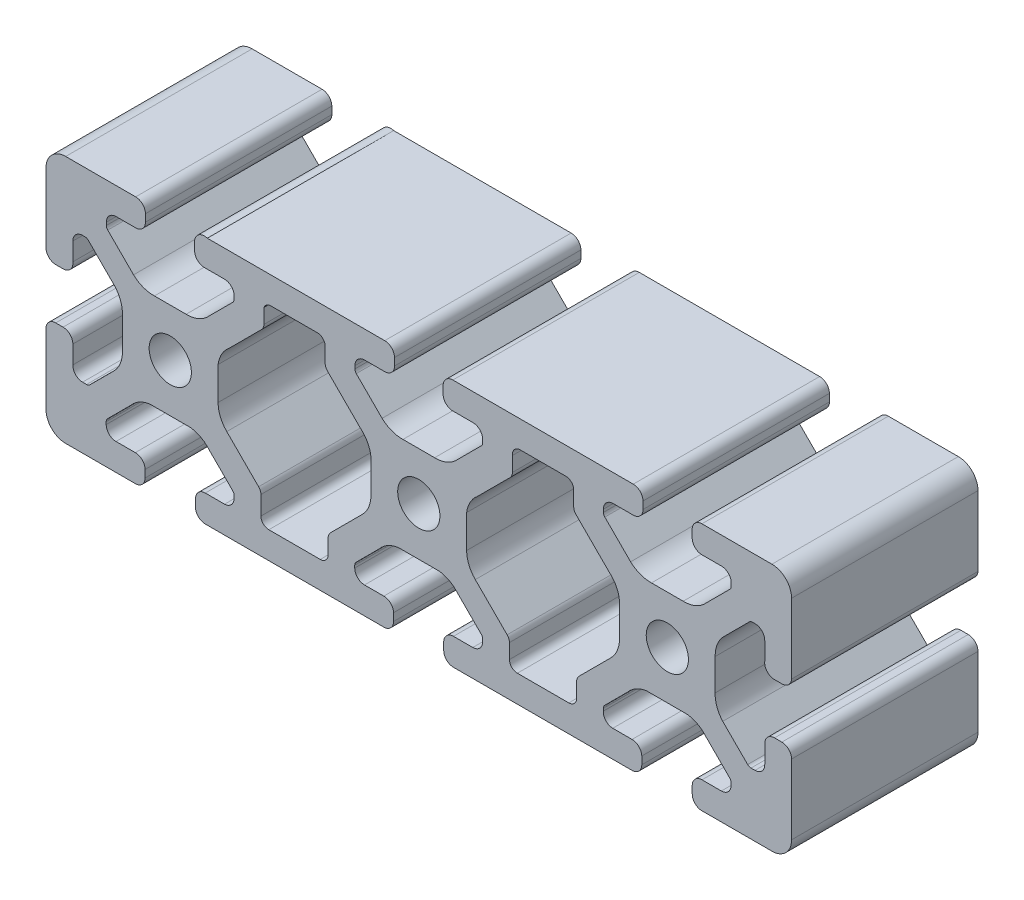
SolidWorks part; units mm, degrees
material "6061 Alloy"
ref_plane "Front Plane" through (0, 0, 0) normal (0, 0, 1) x (1, 0, 0)
ref_plane "Top Plane" through (0, 0, 0) normal (0, 1, 0) x (1, 0, 0)
ref_plane "Right Plane" through (0, 0, 0) normal (1, 0, 0) x (0, 0, -1)
sketch "Sketch1" plane through (0, 0, 0) normal (0, 0, 1) x (1, 0, 0)
  line L0 (-66.9907, 0) -> (65.4005, 0) construction
  line L128 (-34.0397, 20) -> (-5.4835, 20)
  line L129 (-36.0865, 17.2476) -> (-36.0865, 18.4276)
  line L130 (-31.285, 15.68) -> (-34.5165, 15.68)
  line L131 (-29.715, 13.6545) -> (-29.715, 14.11)
  line L132 (-16.3366, 15.68) -> (-23.6634, 15.68)
  line L133 (-24.9334, 14.9061) -> (-24.9334, 12.538)
  line L134 (-25.3054, 11.6399) -> (-30.5988, 6.3465)
  line L135 (-32.3, 3.2591) -> (-32.3, -2.0252)
  line L136 (-14.009, -20) -> (-21.7801, -20)
  line L137 (-19.7616, 20) -> (-19.7616, -25.1394) construction
  line L138 (-24.1394, -15.68) -> (-15.8606, -15.68)
  line L139 (-25.4094, -11.4093) -> (-25.4094, -14.41)
  line L140 (-30.9088, -5.384) -> (-25.7814, -10.5113)
  line L142 (-29.9376, 13.1171) -> (-34.0919, 8.9628)
  line L143 (-37.4506, 7.7) -> (-42.5494, 7.7)
  line L144 (-45.9081, 8.9628) -> (-50.0624, 13.1171)
  line L145 (-50.285, 13.6545) -> (-50.285, 14.11)
  line L146 (-48.715, 15.68) -> (-45.5696, 15.68)
  line L147 (-43.9996, 17.25) -> (-43.9996, 18.43)
  line L148 (-45.5696, 20) -> (-53, 20)
  line L149 (-53, 20) -> (-56.83, 20)
  line L150 (-60, 16.8406) -> (-60, 13.0106)
  line L151 (-60, 13.0106) -> (-60, 5.5825)
  line L152 (-58.3243, 4.1259) -> (-57.1443, 4.1259)
  line L153 (-55.68, 5.8839) -> (-55.68, 8.7865)
  line L154 (-54.11, 10.3565) -> (-53.726, 10.3565)
  line L155 (-53.1886, 10.1339) -> (-49.0111, 5.9564)
  line L156 (-47.7, 2.571) -> (-47.7, -2.502)
  line L157 (-48.9155, -5.8608) -> (-52.9291, -9.8744)
  line L158 (-53.4665, -10.097) -> (-54.111, -10.097)
  line L159 (-55.68, -8.4722) -> (-55.68, -5.5696)
  line L160 (-57.25, -3.9996) -> (-58.43, -3.9996)
  line L161 (-60, -5.5696) -> (-60, -13)
  line L162 (-60, -13) -> (-60, -16.83)
  line L163 (-57.0574, -20) -> (-53.2274, -20)
  line L164 (-53.2274, -20) -> (-45.797, -20)
  line L165 (-44.06, -18.4389) -> (-44.06, -17.25)
  line L166 (-45.63, -15.68) -> (-48.7404, -15.68)
  line L167 (-50.3104, -14.11) -> (-50.3104, -13.7197)
  line L168 (-50.0878, -13.1823) -> (-46.3105, -9.405)
  line L169 (-43.3425, -7.7407) -> (-36.6594, -7.7407)
  line L170 (-33.6914, -9.405) -> (-29.9611, -13.1353)
  line L171 (-29.7385, -13.6727) -> (-29.7385, -14.1108)
  line L172 (-31.2596, -15.68) -> (-34.37, -15.68)
  line L173 (-35.94, -17.25) -> (-35.94, -18.43)
  line L174 (-34.37, -20) -> (-25.991, -20)
  line L175 (-25.991, -20) -> (-21.7801, -20)
  line L176 (-5.63, -20) -> (-14.009, -20)
  line L177 (-4.06, -17.2093) -> (-4.06, -18.43)
  line L178 (-8.7404, -15.68) -> (-5.63, -15.68)
  line L179 (-10.3104, -13.7197) -> (-10.3104, -14.11)
  line L180 (-6.3105, -9.405) -> (-10.0878, -13.1823)
  line L181 (3.3406, -7.7407) -> (-3.3425, -7.7407)
  line L182 (29.9376, 13.1171) -> (34.0919, 8.9628)
  line L183 (3.9116, 17.25) -> (3.9116, 18.43)
  line L184 (8.715, 15.68) -> (5.4816, 15.68)
  line L185 (10.285, 13.6545) -> (10.285, 14.11)
  line L186 (15.0666, 14.2735) -> (15.0666, 11.9054)
  line L187 (14.6946, 11.0074) -> (9.4012, 5.7139)
  line L188 (7.7, 2.6265) -> (7.7, -2.6578)
  line L189 (14.5906, -12.0419) -> (14.5906, -14.41)
  line L190 (9.0912, -6.0165) -> (14.2186, -11.1439)
  line L191 (10.0624, 13.1171) -> (5.9081, 8.9628)
  line L192 (6.3086, -9.405) -> (10.037, -13.1334)
  line L193 (10.2596, -13.6708) -> (10.2596, -14.11)
  line L194 (8.6896, -15.68) -> (5.5792, -15.68)
  line L195 (4.0092, -17.2093) -> (4.0092, -18.43)
  line L196 (5.5792, -20) -> (13.9582, -20)
  line L197 (25.9402, -20) -> (21.7292, -20)
  line L198 (34.3192, -20) -> (25.9402, -20)
  line L199 (35.8892, -17.2093) -> (35.8892, -18.43)
  line L200 (31.2088, -15.68) -> (34.3192, -15.68)
  line L201 (29.6886, -13.6708) -> (29.6886, -14.0552)
  line L202 (33.6397, -9.405) -> (29.9112, -13.1334)
  line L203 (43.2907, -7.7407) -> (36.6076, -7.7407)
  line L204 (50.036, -13.1823) -> (46.2587, -9.405)
  line L205 (50.2586, -14.0552) -> (50.2586, -13.7197)
  line L206 (45.5792, -15.68) -> (48.6896, -15.68)
  line L207 (-2.5494, 7.7) -> (2.5494, 7.7)
  line L208 (-10.0624, 13.1171) -> (-5.9081, 8.9628)
  line L209 (-9.0912, -6.0165) -> (-14.2186, -11.1439)
  line L210 (-14.5906, -12.0419) -> (-14.5906, -14.41)
  line L211 (-7.7, 2.6265) -> (-7.7, -2.6578)
  line L212 (-14.6946, 11.1439) -> (-9.4012, 5.8505)
  line L213 (-15.0666, 14.41) -> (-15.0666, 12.0419)
  line L214 (-10.285, 13.6545) -> (-10.285, 14.11)
  line L215 (-8.715, 15.68) -> (-5.4835, 15.68)
  line L216 (-3.9135, 17.25) -> (-3.9135, 18.43)
  line L217 (-40, 24.8708) -> (-40, -18.43) construction
  line L218 (0, 29.4355) -> (0, -23.1087) construction
  line L219 (-23.0962, 16.9038) -> (-63.6857, -23.6857) construction
  line L220 (-56.2671, 16.2671) -> (-22.7875, -17.2125) construction
  line L221 (44.0092, -18.4389) -> (44.0092, -17.2093)
  line L222 (53.1766, -20) -> (45.7462, -20)
  line L223 (57.0066, -20) -> (53.1766, -20)
  line L224 (60, -13) -> (60, -16.83)
  line L225 (60, -5.5696) -> (60, -13)
  line L226 (57.25, -3.9996) -> (58.43, -3.9996)
  line L227 (55.68, -8.4722) -> (55.68, -5.5696)
  line L228 (53.4665, -10.097) -> (54.111, -10.097)
  line L229 (48.9155, -5.8608) -> (52.9291, -9.8744)
  line L230 (47.7, 2.571) -> (47.7, -2.502)
  line L231 (53.1886, 10.1339) -> (49.0111, 5.9564)
  line L232 (54.11, 10.3565) -> (53.726, 10.3565)
  line L233 (55.68, 5.8839) -> (55.68, 8.7865)
  line L234 (58.3243, 4.1259) -> (57.1443, 4.1259)
  line L235 (60, 13.0106) -> (60, 5.5825)
  line L236 (60, 16.8406) -> (60, 13.0106)
  line L237 (53, 20) -> (56.83, 20)
  line L238 (45.5696, 20) -> (53, 20)
  line L239 (43.9996, 17.25) -> (43.9996, 18.43)
  line L240 (48.715, 15.68) -> (45.5696, 15.68)
  line L241 (50.285, 13.6545) -> (50.285, 14.11)
  line L242 (45.9081, 8.9628) -> (50.0624, 13.1171)
  line L243 (37.4506, 7.7) -> (42.5494, 7.7)
  line L244 (30.9088, -6.0165) -> (25.7814, -11.1439)
  line L245 (25.4094, -12.0419) -> (25.4094, -14.41)
  line L246 (24.1394, -15.68) -> (15.8606, -15.68)
  line L247 (13.9582, -20) -> (21.7292, -20)
  line L248 (32.3, 2.6265) -> (32.3, -2.6578)
  line L249 (25.3054, 11.1439) -> (30.5988, 5.8505)
  line L250 (24.9334, 14.41) -> (24.9334, 12.0419)
  line L251 (16.3366, 15.68) -> (23.6634, 15.68)
  line L252 (29.715, 13.6545) -> (29.715, 14.11)
  line L253 (31.285, 15.68) -> (34.5165, 15.68)
  line L254 (36.0865, 17.25) -> (36.0865, 18.43)
  line L255 (34.5165, 20) -> (5.4816, 20)
  arc A111 (-36.0865, 18.4276) -> (-34.0397, 20) centre (-34.5184, 18.5048) cw
  circle A112 centre (-40, 0) radius 3.4
  arc A113 (-34.5165, 15.68) -> (-36.0865, 17.2476) centre (-34.5165, 17.25) cw
  arc A114 (-31.285, 15.68) -> (-29.715, 14.11) centre (-31.285, 14.11) cw
  arc A115 (-29.715, 13.6545) -> (-29.9376, 13.1171) centre (-30.475, 13.6545) cw
  arc A116 (-32.3, -2.0252) -> (-30.9088, -5.384) centre (-27.55, -2.0252) ccw
  arc A117 (-23.6634, 15.68) -> (-24.9334, 14.9061) centre (-23.7626, 14.4139) ccw
  arc A118 (-25.3054, 11.6399) -> (-24.9334, 12.538) centre (-26.2034, 12.538) ccw
  arc A119 (-30.5988, 6.3465) -> (-32.3, 3.2591) centre (-27.5862, 2.6741) ccw
  arc A120 (-25.4094, -14.41) -> (-24.1394, -15.68) centre (-24.1394, -14.41) ccw
  arc A121 (-25.4094, -11.4093) -> (-25.7814, -10.5113) centre (-26.6794, -11.4093) ccw
  arc A122 (-37.4506, 7.7) -> (-34.0919, 8.9628) centre (-37.3191, 12.4482) ccw
  arc A123 (-45.9081, 8.9628) -> (-42.5494, 7.7) centre (-42.6809, 12.4482) ccw
  arc A124 (-50.285, 13.6545) -> (-50.0624, 13.1171) centre (-49.525, 13.6545) ccw
  arc A125 (-48.715, 15.68) -> (-50.285, 14.11) centre (-48.715, 14.11) ccw
  arc A126 (-45.5696, 15.68) -> (-43.9996, 17.25) centre (-45.5696, 17.25) ccw
  arc A127 (-43.9996, 18.43) -> (-45.5696, 20) centre (-45.5696, 18.43) ccw
  arc A128 (-56.83, 20) -> (-60, 16.8406) centre (-56.83, 16.83) ccw
  arc A129 (-60, 5.5825) -> (-58.3243, 4.1259) centre (-58.4338, 5.692) ccw
  arc A130 (-57.1443, 4.1259) -> (-55.68, 5.8839) centre (-57.2384, 5.693) ccw
  arc A131 (-54.11, 10.3565) -> (-55.68, 8.7865) centre (-54.11, 8.7865) ccw
  arc A132 (-53.1886, 10.1339) -> (-53.726, 10.3565) centre (-53.726, 9.5965) ccw
  arc A133 (-47.7, 2.571) -> (-49.0111, 5.9564) centre (-52.4488, 2.6785) ccw
  arc A134 (-48.9155, -5.8608) -> (-47.7, -2.502) centre (-52.4465, -2.6836) ccw
  arc A135 (-53.4665, -10.097) -> (-52.9291, -9.8744) centre (-53.4665, -9.337) ccw
  arc A136 (-55.68, -8.4722) -> (-54.111, -10.097) centre (-54.111, -8.527) ccw
  arc A137 (-55.68, -5.5696) -> (-57.25, -3.9996) centre (-57.25, -5.5696) ccw
  arc A138 (-58.43, -3.9996) -> (-60, -5.5696) centre (-58.43, -5.5696) ccw
  arc A139 (-60, -16.83) -> (-57.0574, -20) centre (-56.83, -16.8382) ccw
  arc A140 (-45.797, -20) -> (-44.06, -18.4389) centre (-45.63, -18.4389) ccw
  arc A141 (-44.06, -17.25) -> (-45.63, -15.68) centre (-45.63, -17.25) ccw
  arc A142 (-50.3104, -14.11) -> (-48.7404, -15.68) centre (-48.7404, -14.11) ccw
  arc A143 (-50.0878, -13.1823) -> (-50.3104, -13.7197) centre (-49.5504, -13.7197) ccw
  arc A144 (-43.3425, -7.7407) -> (-46.3105, -9.405) centre (-42.6575, -12.4411) ccw
  arc A145 (-33.6914, -9.405) -> (-36.6594, -7.7407) centre (-37.3444, -12.4411) ccw
  arc A146 (-29.7385, -13.6727) -> (-29.9611, -13.1353) centre (-30.4985, -13.6727) ccw
  arc A147 (-31.2596, -15.68) -> (-29.7385, -14.1108) centre (-31.3085, -14.1108) ccw
  arc A148 (-34.37, -15.68) -> (-35.94, -17.25) centre (-34.37, -17.25) ccw
  arc A149 (-35.94, -18.43) -> (-34.37, -20) centre (-34.37, -18.43) ccw
  arc A150 (-4.06, -18.43) -> (-5.63, -20) centre (-5.63, -18.43) cw
  arc A151 (-5.63, -15.68) -> (-4.06, -17.2093) centre (-5.6295, -17.25) cw
  arc A152 (-8.7404, -15.68) -> (-10.3104, -14.11) centre (-8.7404, -14.11) cw
  arc A153 (-10.3104, -13.7197) -> (-10.0878, -13.1823) centre (-9.5504, -13.7197) cw
  arc A154 (-6.3105, -9.405) -> (-3.3425, -7.7407) centre (-2.6575, -12.4411) cw
  arc A155 (3.9116, 18.43) -> (5.4816, 20) centre (5.4816, 18.43) cw
  arc A156 (5.4816, 15.68) -> (3.9116, 17.25) centre (5.4816, 17.25) cw
  arc A157 (8.715, 15.68) -> (10.285, 14.11) centre (8.715, 14.11) cw
  arc A158 (10.285, 13.6545) -> (10.0624, 13.1171) centre (9.525, 13.6545) cw
  arc A159 (7.7, -2.6578) -> (9.0912, -6.0165) centre (12.45, -2.6578) ccw
  arc A160 (16.3366, 15.68) -> (15.0666, 14.2735) centre (16.3292, 14.41) ccw
  arc A161 (14.6946, 11.0074) -> (15.0666, 11.9054) centre (13.7966, 11.9054) ccw
  arc A162 (9.4012, 5.7139) -> (7.7, 2.6265) centre (12.4138, 2.0415) ccw
  arc A163 (14.5906, -14.41) -> (15.8606, -15.68) centre (15.8606, -14.41) ccw
  arc A164 (14.5906, -12.0419) -> (14.2186, -11.1439) centre (13.3206, -12.0419) ccw
  arc A165 (2.5494, 7.7) -> (5.9081, 8.9628) centre (2.6809, 12.4482) ccw
  arc A166 (6.3086, -9.405) -> (3.3406, -7.7407) centre (2.6556, -12.4411) ccw
  arc A167 (10.2596, -13.6708) -> (10.037, -13.1334) centre (9.4996, -13.6708) ccw
  arc A168 (8.6896, -15.68) -> (10.2596, -14.11) centre (8.6896, -14.11) ccw
  arc A169 (5.5792, -15.68) -> (4.0092, -17.2093) centre (5.5787, -17.25) ccw
  arc A170 (4.0092, -18.43) -> (5.5792, -20) centre (5.5792, -18.43) ccw
  arc A171 (35.8892, -18.43) -> (34.3192, -20) centre (34.3192, -18.43) cw
  arc A172 (34.3192, -15.68) -> (35.8892, -17.2093) centre (34.3197, -17.25) cw
  arc A173 (31.2088, -15.68) -> (29.6886, -14.0552) centre (31.2577, -14.1108) cw
  arc A174 (29.6886, -13.6708) -> (29.9112, -13.1334) centre (30.4486, -13.6708) cw
  arc A175 (33.6397, -9.405) -> (36.6076, -7.7407) centre (37.2927, -12.4411) cw
  arc A176 (43.2907, -7.7407) -> (46.2587, -9.405) centre (42.6057, -12.4411) cw
  arc A177 (-2.5494, 7.7) -> (-5.9081, 8.9628) centre (-2.6809, 12.4482) cw
  arc A178 (-14.5906, -12.0419) -> (-14.2186, -11.1439) centre (-13.3206, -12.0419) cw
  arc A179 (-14.5906, -14.41) -> (-15.8606, -15.68) centre (-15.8606, -14.41) cw
  arc A180 (-9.4012, 5.8505) -> (-7.7, 2.6265) centre (-12.43, 2.1914) cw
  arc A181 (-14.6946, 11.1439) -> (-15.0666, 12.0419) centre (-13.7966, 12.0419) cw
  arc A182 (-16.3366, 15.68) -> (-15.0666, 14.41) centre (-16.3366, 14.41) cw
  arc A183 (-7.7, -2.6578) -> (-9.0912, -6.0165) centre (-12.45, -2.6578) cw
  arc A184 (-10.285, 13.6545) -> (-10.0624, 13.1171) centre (-9.525, 13.6545) ccw
  arc A185 (-8.715, 15.68) -> (-10.285, 14.11) centre (-8.715, 14.11) ccw
  arc A186 (-5.4835, 15.68) -> (-3.9135, 17.25) centre (-5.4835, 17.25) ccw
  circle A187 centre (0, 0) radius 3.4
  arc A188 (-3.9135, 18.43) -> (-5.4835, 20) centre (-5.4835, 18.43) ccw
  arc A189 (50.036, -13.1823) -> (50.2586, -13.7197) centre (49.4986, -13.7197) cw
  arc A190 (50.2586, -14.0552) -> (48.6896, -15.68) centre (48.6896, -14.11) cw
  arc A191 (44.0092, -17.2093) -> (45.5792, -15.68) centre (45.5787, -17.25) cw
  arc A192 (45.7462, -20) -> (44.0092, -18.4389) centre (45.5792, -18.4389) cw
  arc A193 (60, -16.83) -> (57.0066, -20) centre (56.83, -16.8349) cw
  arc A194 (58.43, -3.9996) -> (60, -5.5696) centre (58.43, -5.5696) cw
  arc A195 (55.68, -5.5696) -> (57.25, -3.9996) centre (57.25, -5.5696) cw
  arc A196 (55.68, -8.4722) -> (54.111, -10.097) centre (54.111, -8.527) cw
  arc A197 (53.4665, -10.097) -> (52.9291, -9.8744) centre (53.4665, -9.337) cw
  arc A198 (48.9155, -5.8608) -> (47.7, -2.502) centre (52.4465, -2.6836) cw
  arc A199 (47.7, 2.571) -> (49.0111, 5.9564) centre (52.4488, 2.6785) cw
  arc A200 (53.1886, 10.1339) -> (53.726, 10.3565) centre (53.726, 9.5965) cw
  arc A201 (54.11, 10.3565) -> (55.68, 8.7865) centre (54.11, 8.7865) cw
  arc A202 (57.1443, 4.1259) -> (55.68, 5.8839) centre (57.2384, 5.693) cw
  arc A203 (60, 5.5825) -> (58.3243, 4.1259) centre (58.4338, 5.692) cw
  arc A204 (56.83, 20) -> (60, 16.8406) centre (56.83, 16.83) cw
  arc A205 (43.9996, 18.43) -> (45.5696, 20) centre (45.5696, 18.43) cw
  arc A206 (45.5696, 15.68) -> (43.9996, 17.25) centre (45.5696, 17.25) cw
  arc A207 (48.715, 15.68) -> (50.285, 14.11) centre (48.715, 14.11) cw
  arc A208 (50.285, 13.6545) -> (50.0624, 13.1171) centre (49.525, 13.6545) cw
  arc A209 (45.9081, 8.9628) -> (42.5494, 7.7) centre (42.6809, 12.4482) cw
  arc A210 (37.4506, 7.7) -> (34.0919, 8.9628) centre (37.3191, 12.4482) cw
  arc A211 (25.4094, -12.0419) -> (25.7814, -11.1439) centre (26.6794, -12.0419) cw
  arc A212 (25.4094, -14.41) -> (24.1394, -15.68) centre (24.1394, -14.41) cw
  arc A213 (30.5988, 5.8505) -> (32.3, 2.6265) centre (27.57, 2.1914) cw
  arc A214 (25.3054, 11.1439) -> (24.9334, 12.0419) centre (26.2034, 12.0419) cw
  arc A215 (23.6634, 15.68) -> (24.9334, 14.41) centre (23.6634, 14.41) cw
  arc A216 (32.3, -2.6578) -> (30.9088, -6.0165) centre (27.55, -2.6578) cw
  arc A217 (29.715, 13.6545) -> (29.9376, 13.1171) centre (30.475, 13.6545) ccw
  arc A218 (31.285, 15.68) -> (29.715, 14.11) centre (31.285, 14.11) ccw
  arc A219 (34.5165, 15.68) -> (36.0865, 17.25) centre (34.5165, 17.25) ccw
  circle A220 centre (40, 0) radius 3.4
  arc A221 (36.0865, 18.43) -> (34.5165, 20) centre (34.5165, 18.43) ccw
  dimension "D4" = 12.3
  dimension "D11" = 6.8
  dimension "D1" = 40
  dimension "D2" = 40
  dimension "D3" = 120
  dimension "D5" = 20.57
  dimension "D6" = 4.32
  dimension "D7" = 4.32
  dimension "D8" = 4.32
  dimension "D9" = 12.3
  dimension "D10" = 20
  dimension "D12" = 8.12
  dimension "D13" = 4.32
  dimension "D14" = 4.32
extrude "Extrude1" add sketch "Sketch1" against normal blind 30
